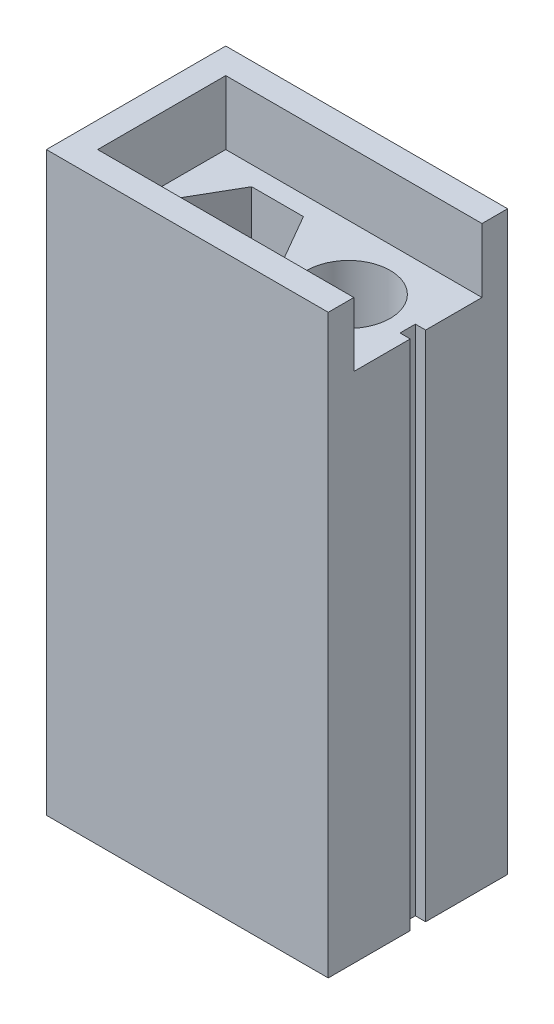
SolidWorks part; units mm, degrees
ref_plane "Front Plane" through (0, 0, 0) normal (0, 0, 1) x (1, 0, 0)
ref_plane "Top Plane" through (0, 0, 0) normal (0, 1, 0) x (1, 0, 0)
ref_plane "Right Plane" through (0, 0, 0) normal (1, 0, 0) x (0, 0, -1)
sketch "Sketch1" plane through (0, 0, 0) normal (0, 1, 0) x (1, 0, 0)
  line L1 (0, 0) -> (22, 0)
  line L2 (0, 0) -> (0, 14)
  line L3 (0, 14) -> (22, 14)
  line L4 (22, 0) -> (22, 14)
  dimension "D1" = 22
  dimension "D2" = 14
extrude "Boss-Extrude1" add sketch "Sketch1" along normal blind 40
sketch "Sketch2" plane through (0, 40, 0) normal (0, 1, 0) x (1, 0, 0)
  line L0 (22, 0) -> (22, 2)
  line L1 (22, 0) -> (22, 14) construction
  line L2 (22, 2) -> (2, 2)
  line L3 (2, 2) -> (2, 12)
  line L4 (2, 12) -> (22, 12)
  line L5 (22, 12) -> (22, 14)
  line L6 (22, 14) -> (0, 14)
  line L7 (0, 14) -> (0, 0)
  line L8 (0, 0) -> (22, 0)
  dimension "D1" = 2
  dimension "D2" = 2
  dimension "D3" = 2
extrude "Boss-Extrude2" add sketch "Sketch2" along normal blind 5
sketch "Sketch3" plane through (0, 40, 0) normal (0, 1, 0) x (1, 0, 0)
  line L0 (2, 2) -> (2, 12) construction
  line L1 (2, 12) -> (22, 12) construction
  line L3 (2, 12) -> (22, 12) construction
  line L4 (0, 7) -> (22, 7) construction
  line L5 (11.5829, 7) -> (9.5622, 10.5)
  line L6 (9.5622, 10.5) -> (5.5207, 10.5)
  line L7 (5.5207, 10.5) -> (3.5, 7)
  line L8 (3.5, 7) -> (5.5207, 3.5)
  line L9 (5.5207, 3.5) -> (9.5622, 3.5)
  line L10 (9.5622, 3.5) -> (11.5829, 7)
  line L11 (0, 14) -> (0, 0) construction
  line L12 (22, 2) -> (22, 12) construction
  circle A0 centre (16.5829, 7) radius 3.25
  circle A1 centre (7.5415, 7) radius 3.5 construction
  dimension "D1" = 6.5
  dimension "D2" = 5
  dimension "D3" = 5
  dimension "D4" = 7
  dimension "D5" = 1.5
  dimension "D6" = 1.5
extrude "Cut-Extrude1" cut sketch "Sketch3" against normal through all
sketch "Sketch4" plane through (22, 0, 0) normal (1, 0, 0) x (0, 0, -1)
  line L0 (7, 45) -> (7, -0.6619) construction
  line L1 (2, 45) -> (12, 45) construction
  line L2 (7, -0.6619) -> (7, 44.794) construction
  line L3 (2, 40) -> (12, 40) construction
  line L4 (6.4, 40) -> (7.6, 40)
  line L5 (6.4, 40) -> (6.4, 0)
  line L6 (6.4, 0) -> (7.6, 0)
  line L7 (7.6, 40) -> (7.6, 0)
  line L8 (0, 0) -> (14, 0) construction
  dimension "D1" = 1.2
  dimension "D2" = 0.6
extrude "Cut-Extrude2" cut sketch "Sketch4" against normal blind 0.8
